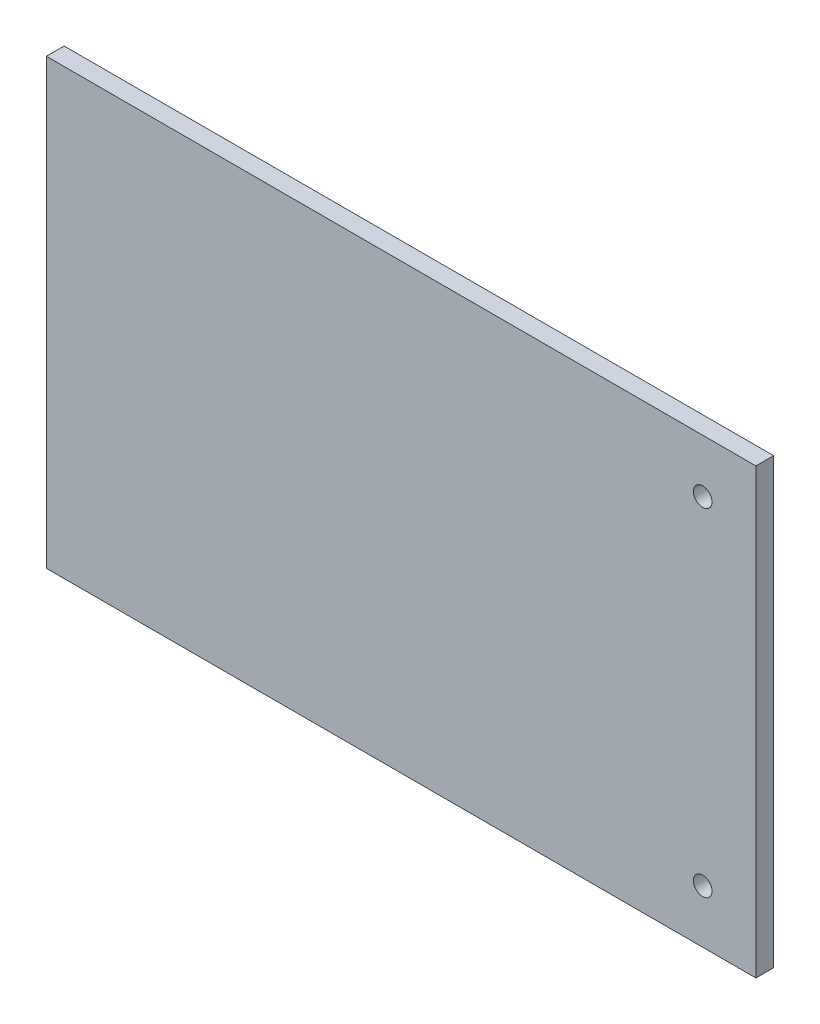
SolidWorks part; units mm, degrees
ref_plane "Ebene vorne" through (0, 0, 0) normal (0, 0, 1) x (1, 0, 0)
ref_plane "Ebene oben" through (0, 0, 0) normal (0, 1, 0) x (1, 0, 0)
ref_plane "Ebene rechts" through (0, 0, 0) normal (1, 0, 0) x (0, 0, -1)
sketch "Skizze1" plane through (0, 0, 0) normal (0, 0, 1) x (1, 0, 0)
  line L1 (200, 125) -> (-200, 125)
  line L2 (200, 125) -> (200, -125)
  line L3 (200, -125) -> (-200, -125)
  line L4 (-200, 125) -> (-200, -125)
  line L5 (200, 125) -> (-200, -125) construction
  line L6 (200, -125) -> (-200, 125) construction
  point P0 (0, 0)
  dimension "D1" = 250
  dimension "D2" = 400
extrude "Aufsatz-Linear austragen1" add sketch "Skizze1" along normal blind 10
hole_wizard "Ø10.5 (10.5) Durchmesser Bohrung1" positions "Skizze2" profile "Skizze3" hole size "Ø10.5" standard "ISO" end condition through all
sketch "Skizze2" plane through (0, 0, 10) normal (0, 0, 1) x (1, 0, 0)
  line L0 (200, 125) -> (-200, 125) construction
  line L1 (200, -125) -> (200, 125) construction
  line L2 (-200, -125) -> (200, -125) construction
  point P0 (170, 95)
  point P2 (170, -95)
  dimension "D1" = 30
  dimension "D2" = 30
  dimension "D3" = 30
  dimension "D4" = 30
sketch "Skizze3" plane through (170, 95, 10) normal (1, 0, 0) x (0, -1, 0)
  line L0 (0, 0) -> (0, 10)
  line L1 (0, 10) -> (5.25, 10)
  line L2 (5.25, 10) -> (5.25, 0)
  line L5 (5.25, 0) -> (0, 0)
  line L11 (0, -6.35) -> (0, 107.95) construction
  dimension "Bohrerdurchmesser" = 10.5
  dimension "Bohrungstiefe" = 10
